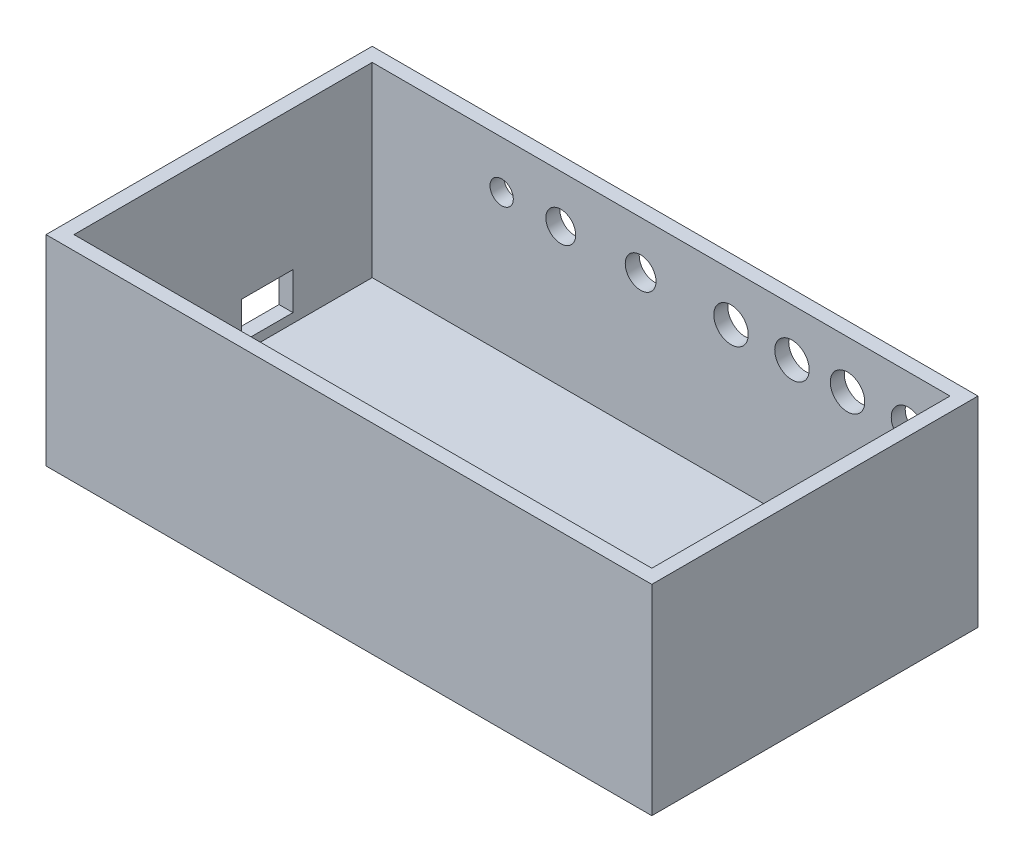
SolidWorks part; units mm, degrees
ref_plane "Front Plane" through (0, 0, 0) normal (0, 0, 1) x (1, 0, 0)
ref_plane "Top Plane" through (0, 0, 0) normal (0, 1, 0) x (1, 0, 0)
ref_plane "Right Plane" through (0, 0, 0) normal (1, 0, 0) x (0, 0, -1)
sketch "Sketch5" plane through (0, 0, 0) normal (0, 1, 0) x (1, 0, 0)
  line L1 (0, -70) -> (130, -70)
  line L2 (0, -70) -> (0, 0)
  line L3 (0, 0) -> (130, 0)
  line L4 (130, -70) -> (130, 0)
extrude "Boss-Extrude3" add sketch "Sketch5" along normal blind 43
sketch "Sketch6" plane through (0, 43, 0) normal (0, 1, 0) x (1, 0, 0)
  line L1 (3, -3) -> (127, -3)
  line L2 (3, -3) -> (3, -67)
  line L3 (3, -67) -> (127, -67)
  line L4 (127, -3) -> (127, -67)
extrude "Cut-Extrude3" cut sketch "Sketch6" against normal blind 40
sketch "Sketch8" plane through (0, 0, 0) normal (0, 0, -1) x (-1, 0, 0)
  line L7 (-130, 43) -> (-30, 43)
  line L8 (-130, 43) -> (0, 43) construction
  circle A0 centre (-118.0814, 32.75) radius 3.7
  circle A1 centre (-105, 32.75) radius 3.7
  circle A2 centre (-93.0814, 32.75) radius 3.7
  circle A3 centre (-80, 32.75) radius 3.7
extrude "Cut-Extrude7" cut sketch "Sketch8" against normal blind 40 contours A1 | A2 | A3 | A0
sketch "Sketch9" plane through (0, 0, 0) normal (0, 0, -1) x (-1, 0, 0)
  line L0 (-118.0814, 32.75) -> (-3.1187, 32.75)
  line L1 (-3.1187, 32.75) -> (0, 32.75)
  line L2 (0, 43) -> (0, 0) construction
  circle A0 centre (-60.6, 32.75) radius 3.3
  circle A1 centre (-43.4661, 32.75) radius 3.2
  circle A2 centre (-30.7817, 32.75) radius 2.5
extrude "Cut-Extrude8" cut sketch "Sketch9" against normal blind 40 contours A0 | A1 | A2
sketch "Sketch10" plane through (0, 0, 0) normal (-1, 0, 0) x (0, 0, 1)
  line L1 (20, 5) -> (31, 5)
  line L2 (20, 5) -> (20, 13)
  line L3 (20, 13) -> (31, 13)
  line L4 (31, 5) -> (31, 13)
extrude "Cut-Extrude9" cut sketch "Sketch10" against normal blind 40 contours L2 L1 L4 L3
